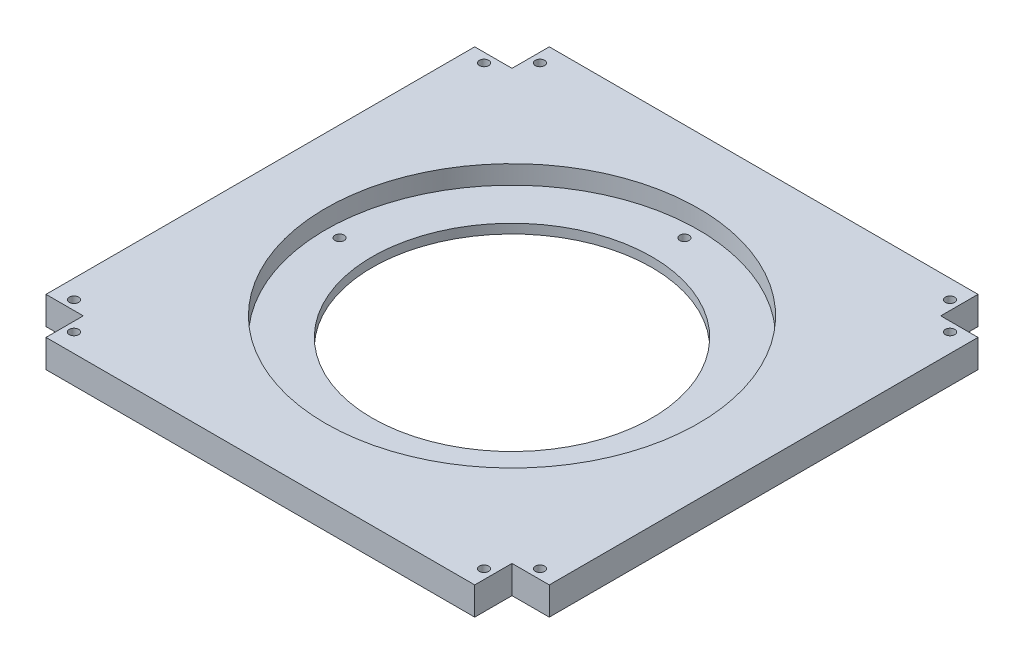
SolidWorks part; units mm, degrees
ref_plane "Front Plane" through (0, 0, 0) normal (0, 0, 1) x (1, 0, 0)
ref_plane "Top Plane" through (0, 0, 0) normal (0, 1, 0) x (1, 0, 0)
ref_plane "Right Plane" through (0, 0, 0) normal (1, 0, 0) x (0, 0, -1)
sketch "Sketch1" plane through (0, 0, 0) normal (0, 1, 0) x (1, 0, 0)
  line L21 (0, 0) -> (270, 0)
  line L22 (0, 0) -> (0, 270)
  line L23 (0, 270) -> (270, 270)
  line L24 (270, 0) -> (270, 270)
  line L44 (135, 270) -> (135, 0) construction
  line L45 (0, 135) -> (270, 135) construction
  dimension "D1" = 270
  dimension "D2" = 270
extrude "Boss-Extrude1" add sketch "Sketch1" along normal blind 15
sketch "Sketch8" plane through (0, 15, 0) normal (0, 1, 0) x (1, 0, 0)
  line L1 (0, 270) -> (20, 270)
  line L2 (0, 270) -> (0, 250)
  line L3 (0, 250) -> (20, 250)
  line L4 (20, 270) -> (20, 250)
  line L5 (270, 270) -> (250, 270)
  line L6 (270, 270) -> (270, 250)
  line L7 (270, 250) -> (250, 250)
  line L8 (250, 270) -> (250, 250)
  line L9 (270, 0) -> (250, 0)
  line L10 (270, 0) -> (270, 20)
  line L11 (270, 20) -> (250, 20)
  line L12 (250, 0) -> (250, 20)
  line L13 (0, 0) -> (20, 0)
  line L14 (0, 0) -> (0, 20)
  line L15 (0, 20) -> (20, 20)
  line L16 (20, 0) -> (20, 20)
  dimension "D1" = 20
  dimension "D2" = 20
  dimension "D3" = 20
  dimension "D4" = 20
  dimension "D5" = 20
  dimension "D6" = 20
  dimension "D7" = 20
  dimension "D8" = 20
extrude "Cut-Extrude1" cut sketch "Sketch8" against normal through all
sketch "Sketch9" plane through (0, 15, 0) normal (0, 1, 0) x (1, 0, 0)
  line L0 (135, 270) -> (135, 0) construction
  line L1 (250, 270) -> (20, 270) construction
  line L2 (20, 0) -> (250, 0) construction
  line L3 (0, 135) -> (270, 135) construction
  line L4 (0, 250) -> (0, 20) construction
  line L5 (270, 20) -> (270, 250) construction
  line L6 (260, 250) -> (260, 20) construction
  line L7 (250, 250) -> (270, 250) construction
  line L8 (270, 20) -> (250, 20) construction
  line L9 (250, 10) -> (20, 10) construction
  line L10 (250, 20) -> (250, 0) construction
  line L11 (20, 0) -> (20, 20) construction
  line L12 (10, 250) -> (10, 20) construction
  line L13 (0, 250) -> (20, 250) construction
  line L14 (20, 20) -> (0, 20) construction
  line L15 (20, 260) -> (250, 260) construction
  line L16 (20, 250) -> (20, 270) construction
  line L17 (250, 270) -> (250, 250) construction
  circle A0 centre (10, 245) radius 2.5
  circle A1 centre (10, 25) radius 2.5
  circle A2 centre (25, 10) radius 2.5
  circle A3 centre (245, 10) radius 2.5
  circle A4 centre (260, 25) radius 2.5
  circle A5 centre (260, 245) radius 2.5
  circle A6 centre (245, 260) radius 2.5
  circle A7 centre (25, 260) radius 2.5
  dimension "D1" = 5
  dimension "D2" = 5
  dimension "D3" = 5
  dimension "D4" = 5
  dimension "D5" = 5
  dimension "D6" = 5
  dimension "D7" = 5
  dimension "D8" = 5
  dimension "D9" = 5
  dimension "D10" = 5
  dimension "D11" = 5
  dimension "D12" = 5
  dimension "D13" = 5
  dimension "D14" = 5
  dimension "D15" = 5
  dimension "D16" = 5
extrude "Cut-Extrude2" cut sketch "Sketch9" against normal through all
sketch "Sketch10" plane through (0, 15, 0) normal (0, 1, 0) x (1, 0, 0)
  line L0 (135, 270) -> (135, 0) construction
  line L2 (250, 270) -> (20, 270) construction
  line L3 (20, 0) -> (250, 0) construction
  line L4 (0, 135) -> (270, 135) construction
  line L5 (0, 250) -> (0, 20) construction
  line L6 (270, 20) -> (270, 250) construction
  circle A0 centre (135, 135) radius 100
  dimension "D1" = 200
extrude "Cut-Extrude3" cut sketch "Sketch10" against normal blind 10
sketch "Sketch12" plane through (0, 5, 0) normal (0, 1, 0) x (1, 0, 0)
  line L0 (135, 235) -> (135, 35) construction
  line L1 (35, 135) -> (235, 135) construction
  circle A0 centre (135, 135) radius 100 construction
  circle A1 centre (135, 135) radius 100 construction
  circle A2 centre (135, 135) radius 75
  circle A3 centre (135, 227.5) radius 2.5
  circle A4 centre (227.5, 135) radius 2.5
  circle A5 centre (135, 42.5) radius 2.5
  circle A6 centre (42.5, 135) radius 2.5
  dimension "D1" = 150
  dimension "D2" = 5
  dimension "D3" = 5
  dimension "D4" = 5
  dimension "D5" = 5
  dimension "D6" = 92.5
  dimension "D7" = 92.5
  dimension "D8" = 92.5
  dimension "D9" = 92.5
extrude "Cut-Extrude4" cut sketch "Sketch12" against normal through all
sketch "Sketch13" plane through (0, 15, 0) normal (0, 1, 0) x (1, 0, 0)
  line L0 (135, 270) -> (135, 0) construction
  line L1 (250, 270) -> (20, 270) construction
  line L2 (20, 0) -> (250, 0) construction
  line L3 (0, 135) -> (270, 135) construction
  line L4 (0, 250) -> (0, 20) construction
  line L5 (270, 20) -> (270, 250) construction
  line L7 (110, 0) -> (160, 0)
  line L8 (110, 0) -> (110, 20)
  line L9 (110, 20) -> (160, 20)
  line L10 (160, 0) -> (160, 20)
  dimension "D1" = 20
  dimension "D2" = 50
  dimension "D3" = 25
  dimension "D4" = 25
